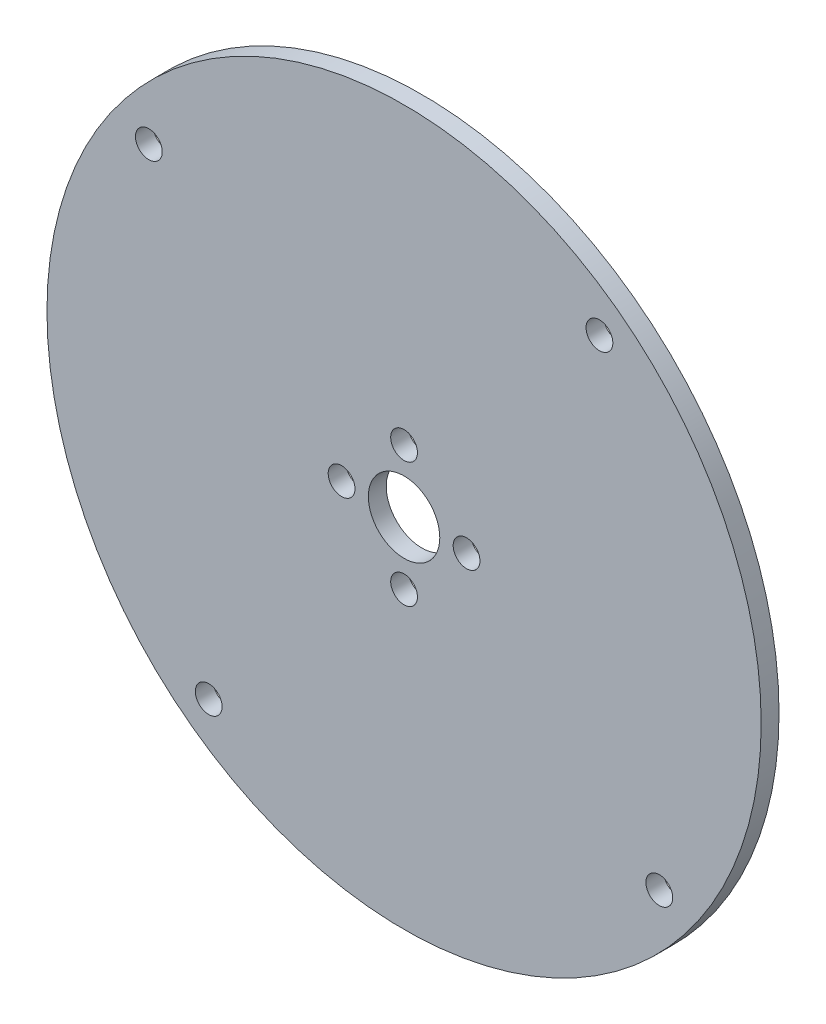
SolidWorks part; units mm, degrees
ref_plane "前视基准面" through (0, 0, 0) normal (0, 0, 1) x (1, 0, 0)
ref_plane "上视基准面" through (0, 0, 0) normal (0, 1, 0) x (1, 0, 0)
ref_plane "右视基准面" through (0, 0, 0) normal (1, 0, 0) x (0, 0, -1)
sketch "草图3" plane through (0, 0, 0) normal (0, 0, 1) x (1, 0, 0)
  line L0 (21.8824, 28.586) -> (-21.8824, -28.586) construction
  line L1 (28.586, -21.8824) -> (-28.586, 21.8824) construction
  circle A0 centre (0, 0) radius 40
  circle A1 centre (0, 0) radius 4
  circle A2 centre (0, 7) radius 1.5
  circle A3 centre (0, -7) radius 1.5
  circle A4 centre (-7, 0) radius 1.5
  circle A5 centre (7, 0) radius 1.5
  circle A6 centre (-28.586, 21.8824) radius 1.5
  circle A7 centre (21.8824, 28.586) radius 1.5
  circle A8 centre (-21.8824, -28.586) radius 1.5
  circle A9 centre (28.586, -21.8824) radius 1.5
  dimension "D1" = 80
  dimension "D2" = 8
  dimension "D7" = 3
  dimension "D8" = 3
  dimension "D9" = 3
  dimension "D10" = 3
  dimension "D15" = 3
  dimension "D16" = 3
  dimension "D17" = 3
  dimension "D18" = 3
  dimension "D3" = 7
  dimension "D4" = 7
  dimension "D5" = 7
  dimension "D6" = 7
  dimension "D11" = 36
  dimension "D12" = 36
  dimension "D13" = 36
  dimension "D14" = 36
extrude "凸台-拉伸1" add sketch "草图3" along normal blind 2
